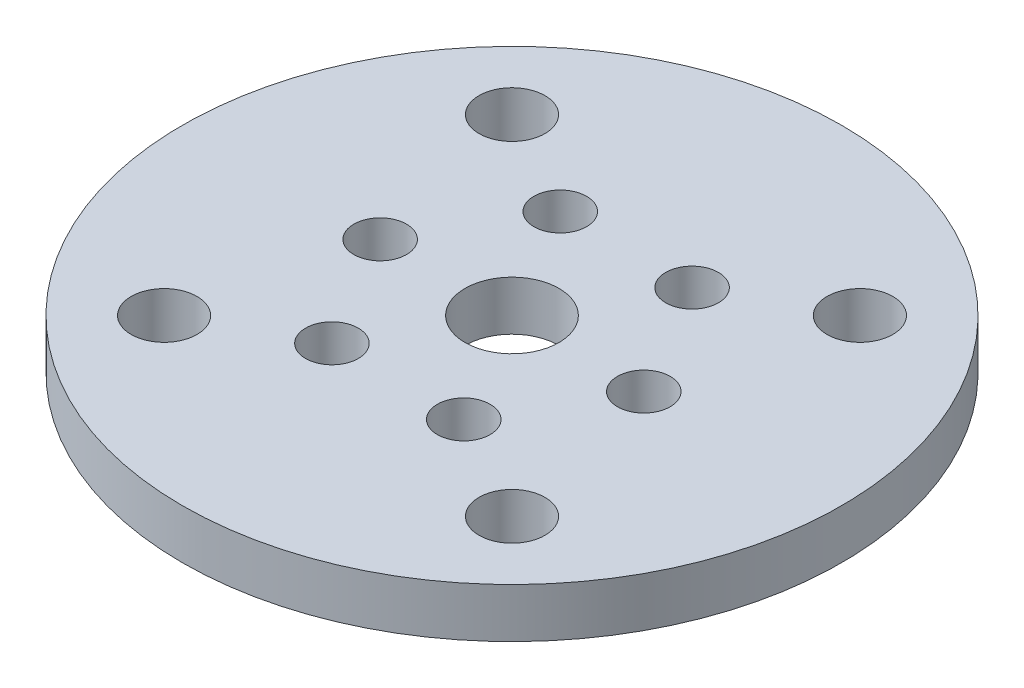
SolidWorks part; units mm, degrees
material "Policarbonato"
ref_plane "Plano frontal" through (0, 0, 0) normal (0, 0, 1) x (1, 0, 0)
ref_plane "Plano superior" through (0, 0, 0) normal (0, 1, 0) x (1, 0, 0)
ref_plane "Plano direito" through (0, 0, 0) normal (1, 0, 0) x (0, 0, -1)
ref_plane "Plano1" through (0, -3, 0) normal (0, -1, 0) x (1, 0, 0)
sketch "Esboço1" plane through (0, -3, 0) normal (0, -1, 0) x (1, 0, 0)
  circle A0 centre (0, 0) radius 2.85
  circle A1 centre (10.5571, 10.5571) radius 2
  circle A2 centre (10.5571, -10.5571) radius 2
  circle A3 centre (-10.5571, -10.5571) radius 2
  circle A4 centre (-10.5571, 10.5571) radius 2
  circle A5 centre (0, 0) radius 20
  circle A6 centre (-8, 0) radius 1.6
  circle A7 centre (-4, 6.9282) radius 1.6
  circle A8 centre (4, 6.9282) radius 1.6
  circle A9 centre (8, 0) radius 1.6
  circle A10 centre (4, -6.9282) radius 1.6
  circle A11 centre (-4, -6.9282) radius 1.6
  point P14 (0, 0)
  point P26 (0, 0)
  dimension "D1" = 4
  dimension "D2" = 40
  dimension "D3" = 5.7
  dimension "D8" = 3.2
  dimension "D4" = 14.93
  dimension "D7" = 16
  dimension "D5" = 4
  dimension "D6" = 6
extrude "Ressalto-extrusão1" add sketch "Esboço1" against normal blind 3
